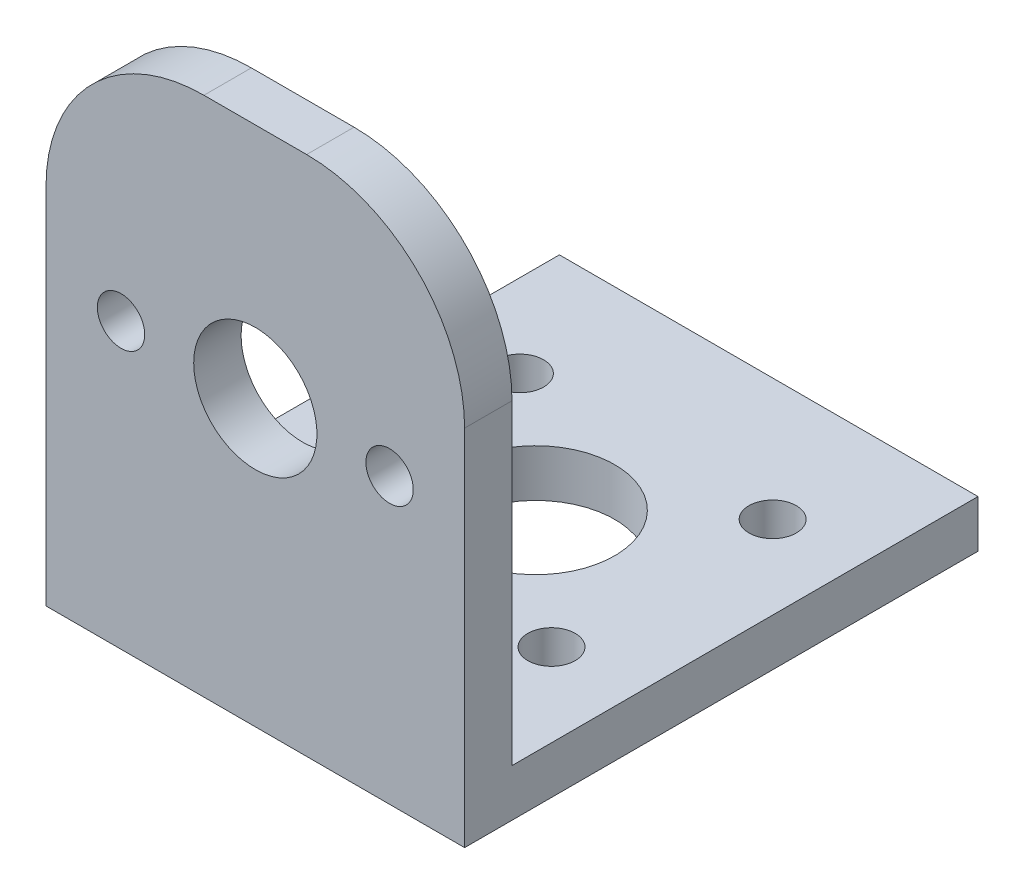
SolidWorks part; units mm, degrees
ref_plane "Front Plane" through (0, 0, 0) normal (0, 0, 1) x (1, 0, 0)
ref_plane "Top Plane" through (0, 0, 0) normal (0, 1, 0) x (1, 0, 0)
ref_plane "Right Plane" through (0, 0, 0) normal (1, 0, 0) x (0, 0, -1)
sketch "Sketch1" plane through (0, 0, 0) normal (1, 0, 0) x (0, 0, -1)
  line L3 (-3, -3) -> (29.5, -3)
  line L4 (29.5, -3) -> (29.5, 0)
  line L5 (29.5, 0) -> (0, 0)
  line L6 (-3, -3) -> (-3, 30)
  line L7 (-3, 30) -> (0, 30)
  line L8 (0, 30) -> (0, 0)
  dimension "D1" = 32.5
  dimension "D2" = 33
  dimension "D3" = 3
  dimension "D4" = 3
extrude "Boss-Extrude1" add sketch "Sketch1" along normal blind 26.5
sketch "Sketch2" plane through (0, 0, 0) normal (0, 0, -1) x (-1, 0, 0)
  line L0 (-13.25, 30) -> (-13.25, 0) construction
  line L1 (-16.5, 30) -> (-10, 30)
  line L5 (-21.75, 15) -> (-4.75, 15) construction
  arc A0 (-10, 30) -> (0, 20) centre (-10, 20) cw
  arc A1 (-16.5, 30) -> (-26.5, 20) centre (-16.5, 20) ccw
  circle A2 centre (-13.25, 15) radius 12.5 construction
  circle A3 centre (-13.25, 15) radius 3.9
  circle A4 centre (-4.75, 15) radius 1.5
  circle A5 centre (-21.75, 15) radius 1.5
  point P10 (-26.5, 30)
  point P19 (-13.25, 15)
  line M12 (0, 0) -> (0, 30)
  line M13 (0, 30) -> (-26.5, 30)
  line M14 (-26.5, 30) -> (-26.5, 0)
  dimension "D1" = 10
  dimension "D2" = 25
  dimension "D3" = 3
  dimension "D4" = 7.8
  dimension "D5" = 3
  dimension "D6" = 17
extrude "Cut-Extrude1" cut sketch "Sketch2" against normal through all contours A3 | A4 | A5 | A1 M13 M14 | A0 M13 M12
sketch "Sketch3" plane through (0, 0, 0) normal (0, 1, 0) x (1, 0, 0)
  line L0 (13.25, 29.5) -> (13.25, 0) construction
  line L1 (26.5, 29.5) -> (0, 29.5) construction
  line L2 (16.5, 0) -> (10, 0) construction
  line L4 (5.25, 21.75) -> (21.25, 21.75) construction
  line L5 (5.25, 21.75) -> (5.25, 7.75) construction
  line L6 (5.25, 7.75) -> (21.25, 7.75) construction
  line L7 (21.25, 21.75) -> (21.25, 7.75) construction
  line L8 (5.25, 21.75) -> (21.25, 7.75) construction
  line L9 (5.25, 7.75) -> (21.25, 21.75) construction
  circle A0 centre (13.25, 14.75) radius 5
  circle A1 centre (21.25, 21.75) radius 1.5
  circle A2 centre (21.25, 7.75) radius 1.5
  circle A3 centre (5.25, 21.75) radius 1.5
  circle A4 centre (5.25, 7.75) radius 1.5
extrude "Cut-Extrude2" cut sketch "Sketch3" against normal through all
sketch "Sketch4" plane through (0, -3, 0) normal (0, -1, 0) x (1, 0, 0)
  line L1 (0, 3) -> (26.5, 3) construction
  line L2 (0, 3) -> (0, -29.5) construction
  line L3 (0, -29.5) -> (26.5, -29.5) construction
  line L4 (26.5, 3) -> (26.5, -29.5) construction
